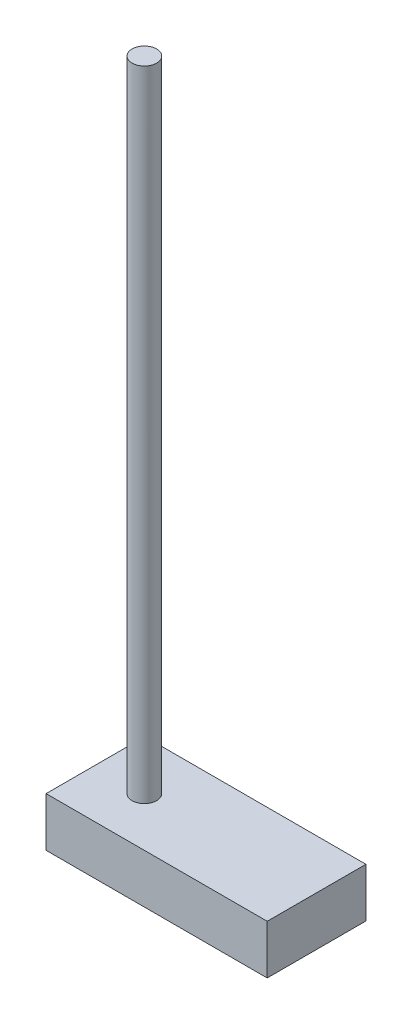
SolidWorks part; units mm, degrees
ref_plane "Alzado" through (0, 0, 0) normal (0, 0, 1) x (1, 0, 0)
ref_plane "Planta" through (0, 0, 0) normal (0, 1, 0) x (1, 0, 0)
ref_plane "Vista lateral" through (0, 0, 0) normal (1, 0, 0) x (0, 0, -1)
sketch "Croquis1" plane through (0, 0, 0) normal (0, 1, 0) x (1, 0, 0)
  circle A0 centre (0, 0) radius 2.5
extrude "Saliente-Extruir1" add sketch "Croquis1" along normal blind 20
sketch "Croquis2" plane through (0, 0, 0) normal (0, -1, 0) x (1, 0, 0)
  line L0 (35, -119.5948) -> (35, 38.4052) construction
  line L1 (-10, 10) -> (35, 10)
  line L2 (-10, 10) -> (-10, -10.0876)
  line L3 (-10, -10.0876) -> (35, -10.0876)
  line L4 (35, 10) -> (35, -10.0876)
  dimension "D1" = 20.0876
  dimension "D2" = 10
  dimension "D3" = 10
extrude "Saliente-Extruir2" add sketch "Croquis2" along normal blind 10
sketch "Croquis3" plane through (0, 20, 0) normal (0, 1, 0) x (1, 0, 0)
  circle A0 centre (0, 0) radius 2.5
extrude "Saliente-Extruir3" add sketch "Croquis3" along normal blind 110
